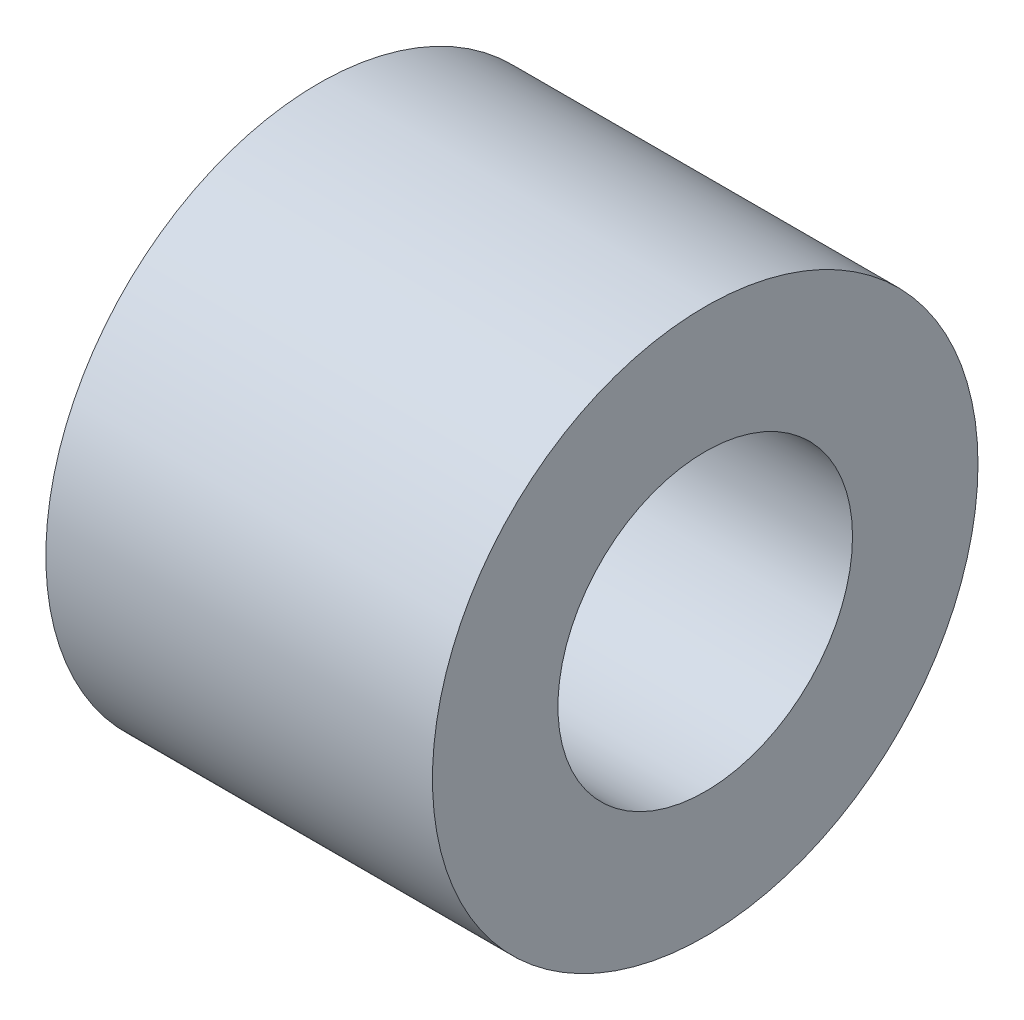
SolidWorks part; units mm, degrees
ref_plane "Plan de face" through (0, 0, 0) normal (0, 0, 1) x (1, 0, 0)
ref_plane "Plan de dessus" through (0, 0, 0) normal (0, 1, 0) x (1, 0, 0)
ref_plane "Plan de droite" through (0, 0, 0) normal (1, 0, 0) x (0, 0, -1)
sketch "Esquisse1" plane through (0, 0, 0) normal (1, 0, 0) x (0, 0, -1)
  circle A0 centre (0, 0) radius 3.429
  circle A1 centre (0, 0) radius 6.35
  dimension "D1" = 6.858
  dimension "D2" = 12.7
extrude "Boss.-Extru.1" add sketch "Esquisse1" against normal blind 9
equation "\"D1@Boss.-Extru.1\"=9mm"
